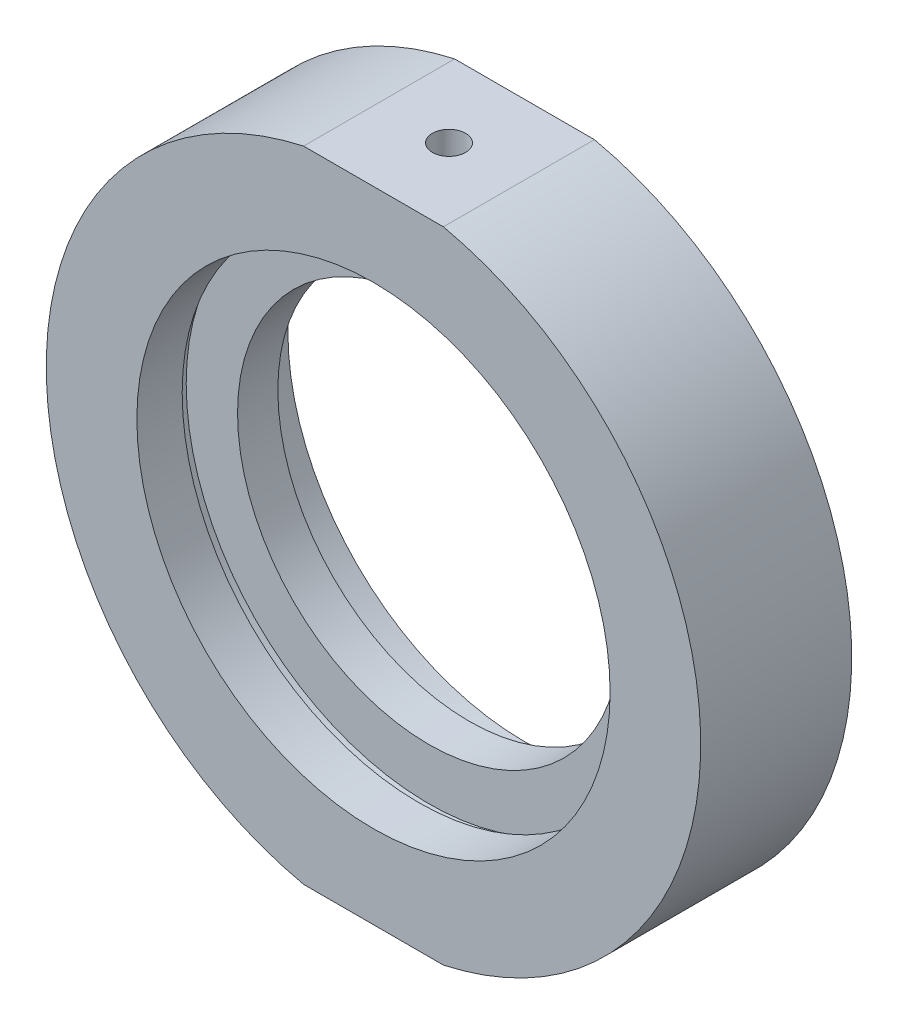
SolidWorks part; units mm, degrees
ref_plane "前视基准面" through (0, 0, 0) normal (0, 0, 1) x (1, 0, 0)
ref_plane "上视基准面" through (0, 0, 0) normal (0, 1, 0) x (1, 0, 0)
ref_plane "右视基准面" through (0, 0, 0) normal (1, 0, 0) x (0, 0, -1)
sketch "草图1" plane through (0, 0, 0) normal (0, 1, 0) x (1, 0, 0)
  line L0 (0, 31.9391) -> (0, -26.491) construction
  line L1 (32.5, 7.5) -> (32.5, -7.5)
  line L3 (24.1, 2) -> (24.1, 3)
  line L4 (24.1, 3) -> (23.5, 3)
  line L6 (32.5, -7.5) -> (23.5, -7.5)
  line L7 (23.5, -7.5) -> (23.5, -3)
  line L8 (24.1, -2) -> (19, -2)
  line L9 (19, -2) -> (19, 2)
  line L10 (19, 2) -> (24.1, 2)
  line L11 (23.5, 3) -> (23.5, 7.5)
  line L12 (23.5, 7.5) -> (32.5, 7.5)
  line L13 (24.1, -2) -> (24.1, -3)
  line L14 (24.1, -3) -> (23.5, -3)
  line L17 (35.331, 0) -> (-5.0345, 0) construction
  point P3 (24.0113, 2)
  point P6 (19, 0)
  point P14 (0, 0)
  point P16 (35.331, 0)
  point P19 (22.9383, 2)
  point P22 (24.6459, 2)
  point P23 (24.1469, 2)
  point P24 (0, 0)
  dimension "D2" = 19
  dimension "D3" = 23.5
  dimension "D4" = 23.5
  dimension "D5" = 15
  dimension "D6" = 5.5
  dimension "D7" = 5.5
  dimension "D8" = 24.1
  dimension "D9" = 32.5
  dimension "D10" = 24.1
  dimension "D11" = 1
  dimension "D12" = 1
  dimension "D13" = 7.5
  dimension "D18" = 0
revolve "旋转1" add sketch "草图1" angle 360 about L0
cosmetic thread "装饰螺纹线1" parameters "D2"=48
cosmetic thread "装饰螺纹线2" parameters "D2"=48
sketch "草图2" plane through (0, 0, 7.5) normal (0, 0, 1) x (1, 0, 0)
  line L0 (0, 0) -> (43.1523, 0) construction
  line L1 (-33.152, 40.9989) -> (30.8698, 40.9989)
  line L2 (-33.152, 40.9989) -> (-33.152, 31.75)
  line L3 (-33.152, 31.75) -> (30.8698, 31.75)
  line L4 (30.8698, 40.9989) -> (30.8698, 31.75)
  line L5 (30.8698, -40.9989) -> (30.8698, -31.75)
  line L6 (-33.152, -31.75) -> (30.8698, -31.75)
  line L7 (-33.152, -40.9989) -> (-33.152, -31.75)
  line L8 (-33.152, -40.9989) -> (30.8698, -40.9989)
  dimension "D1" = 31.75
extrude "切除-拉伸1" cut sketch "草图2" against normal blind 49
sketch "草图10" plane through (0, 0, 0) normal (0, 0, 1) x (1, 0, 0)
  line L0 (0, 31.75) -> (0, -31.75)
  line L1 (-6.9417, 31.75) -> (6.9417, 31.75) construction
  line L2 (-6.9417, -31.75) -> (6.9417, -31.75) construction
  line L3 (0, 0) -> (-28.1458, 16.25)
  line L4 (0, 0) -> (28.1458, 16.25)
  arc A2 (6.9417, -31.75) -> (6.9417, 31.75) centre (0, 0) ccw construction
  arc A3 (-6.9417, 31.75) -> (-6.9417, -31.75) centre (0, 0) ccw construction
  arc A4 (28.1458, 16.25) -> (6.9417, 31.75) centre (0, 0) ccw
  arc A5 (-6.9417, 31.75) -> (-28.1458, 16.25) centre (0, 0) ccw
  dimension "D1" = 60
  dimension "D2" = 60
hole_wizard "M4 螺纹孔2" positions "草图15" profile "草图16" tap size "M4" standard "ISO"
sketch "草图15" plane through (0, 31.75, 0) normal (0, 1, 0) x (1, 0, 0)
  point P0 (0, 0)
sketch "草图16" plane through (0, 31.75, 0) normal (1, 0, 0) x (0, 0, 1)
  line L0 (0, 0) -> (0, 6.4914)
  line L1 (0, 6.4914) -> (1.65, 5.5)
  line L2 (1.65, 5.5) -> (1.65, 0)
  line L5 (1.65, 0) -> (0, 0)
  line L10 (0, 6.4914) -> (-1.65, 5.5) construction
  line L11 (0, -6.35) -> (0, 107.95) construction
  dimension "螺纹孔钻头直径" = 3.3
  dimension "螺纹孔钻头深度" = 5.5
  dimension "导头角度" = 118
cosmetic thread "孔螺蚊线6" parameters "D1"=5.5, "D2"=4
hole_wizard "M6 螺纹孔2" positions "草图17" profile "草图18" tap size "M6" standard "ISO"
sketch "草图17" plane through (0, -31.75, 0) normal (0, -1, 0) x (-1, 0, 0)
  point P0 (0, 0)
sketch "草图18" plane through (0, -31.75, 0) normal (1, 0, 0) x (0, 0, -1)
  line L0 (0, 0) -> (0, 7.0022)
  line L1 (0, 7.0022) -> (2.5, 5.5)
  line L2 (2.5, 5.5) -> (2.5, 0)
  line L5 (2.5, 0) -> (0, 0)
  line L10 (0, 7.0022) -> (-2.5, 5.5) construction
  line L11 (0, -6.35) -> (0, 107.95) construction
  dimension "螺纹孔钻头直径" = 5
  dimension "螺纹孔钻头深度" = 5.5
  dimension "导头角度" = 118
cosmetic thread "孔螺蚊线7" parameters "D1"=5.5, "D2"=6
